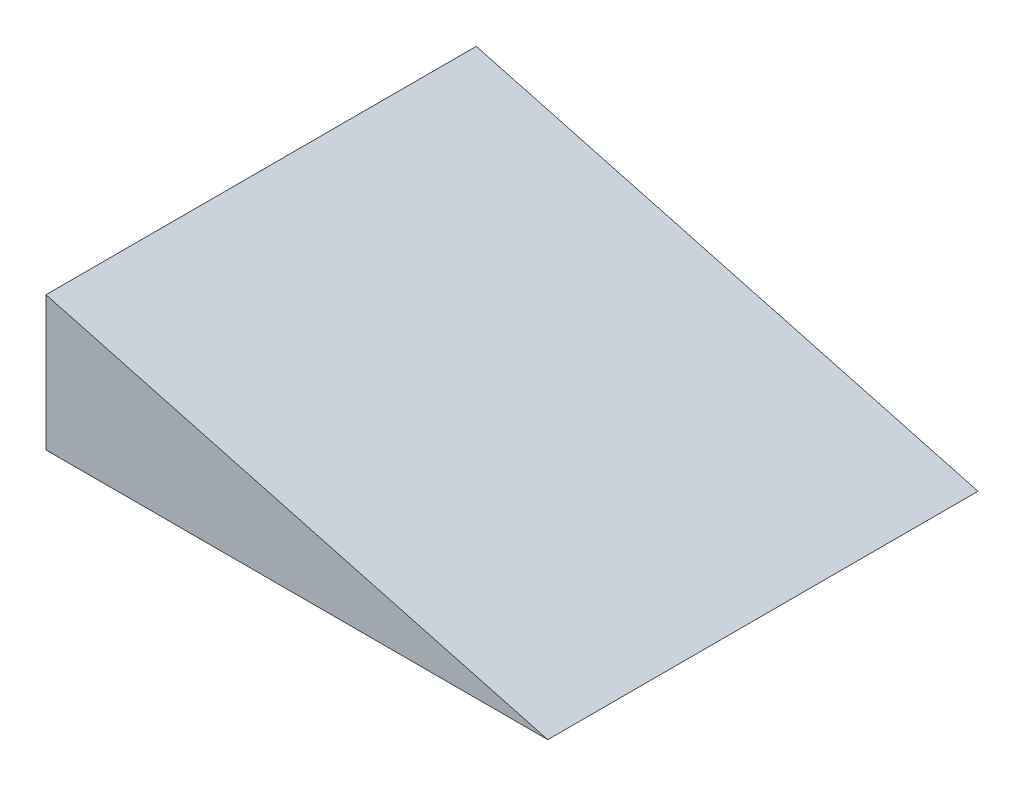
SolidWorks part; units mm, degrees
material "Maple"
ref_plane "Front Plane" through (0, 0, 0) normal (0, 0, 1) x (1, 0, 0)
ref_plane "Top Plane" through (0, 0, 0) normal (0, 1, 0) x (1, 0, 0)
ref_plane "Right Plane" through (0, 0, 0) normal (1, 0, 0) x (0, 0, -1)
sketch "Sketch1" plane through (0, 0, 0) normal (0, 0, 1) x (1, 0, 0)
  line L0 (0, 0) -> (0, 127)
  line L1 (0, 127) -> (473.9705, 0)
  line L2 (473.9705, 0) -> (0, 0)
  dimension "D1" = 15
  dimension "D2" = 127
extrude "Boss-Extrude1" add sketch "Sketch1" against normal blind 406.4
